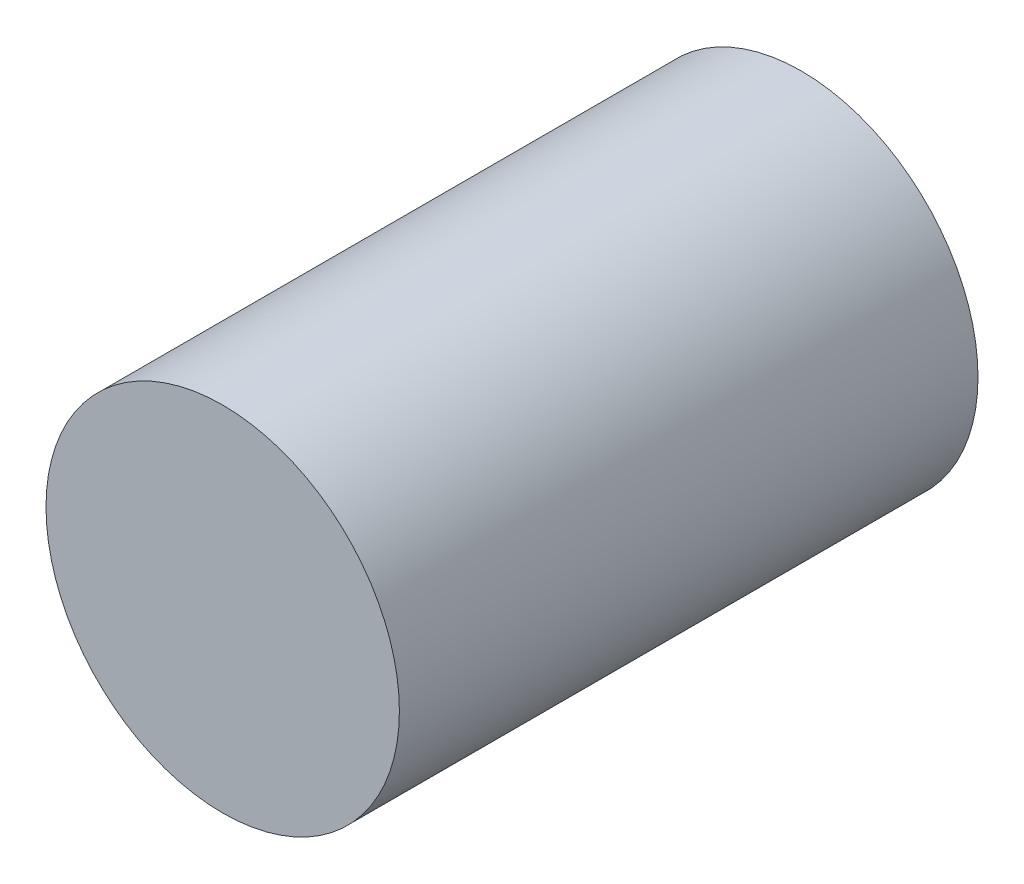
SolidWorks part; units mm, degrees
ref_plane "Ebene vorne" through (0, 0, 0) normal (0, 0, 1) x (1, 0, 0)
ref_plane "Ebene oben" through (0, 0, 0) normal (0, 1, 0) x (1, 0, 0)
ref_plane "Ebene rechts" through (0, 0, 0) normal (1, 0, 0) x (0, 0, -1)
sketch "Skizze1" plane through (0, 0, 0) normal (0, 0, 1) x (1, 0, 0)
  circle A0 centre (0, 0) radius 28.4
  dimension "D1" = 56.8
extrude "Aufsatz-Linear austragen1" add sketch "Skizze1" along normal blind 93
